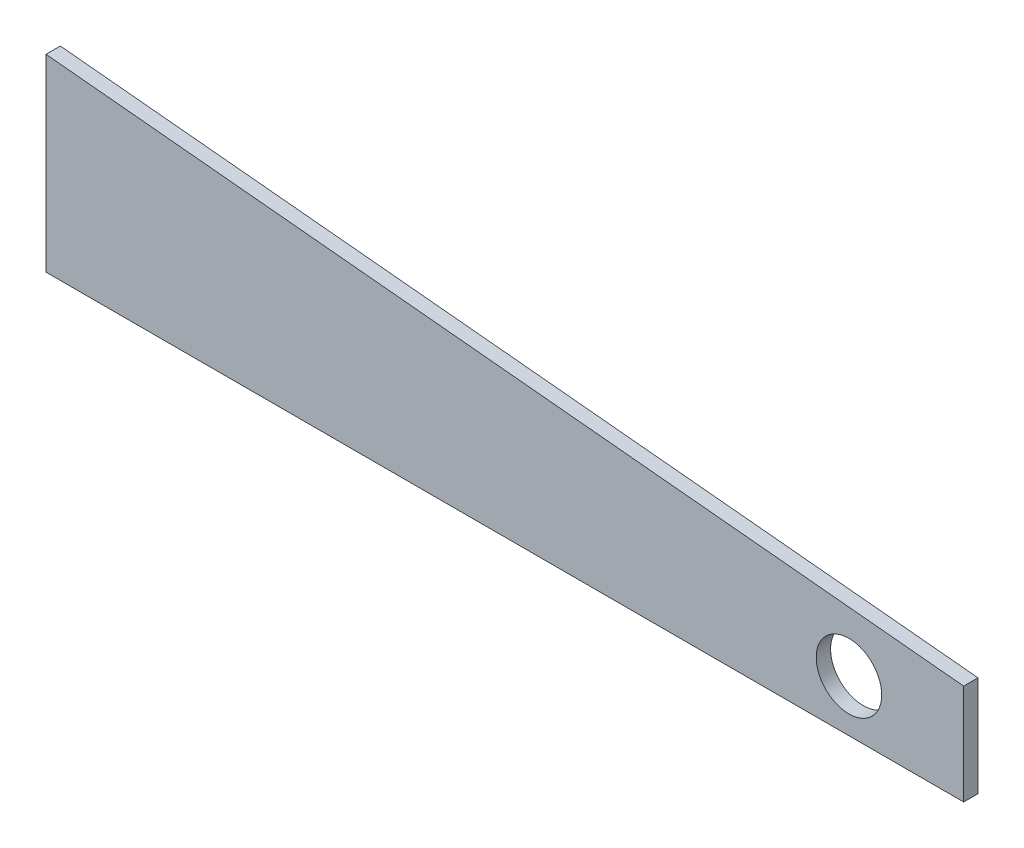
SolidWorks part; units mm, degrees
ref_plane "Front Plane" through (0, 0, 0) normal (0, 0, 1) x (1, 0, 0)
ref_plane "Top Plane" through (0, 0, 0) normal (0, 1, 0) x (1, 0, 0)
ref_plane "Right Plane" through (0, 0, 0) normal (1, 0, 0) x (0, 0, -1)
sketch "Sketch1" plane through (0, 0, 0) normal (0, 0, 1) x (1, 0, 0)
  line L0 (0, 0) -> (406.4, 0)
  line L1 (406.4, 0) -> (406.4, 44.45)
  line L2 (406.4, 44.45) -> (0, 83.566)
  line L3 (0, 83.566) -> (0, 0)
  dimension "D1" = 406.4
  dimension "D2" = 44.45
  dimension "D3" = 83.566
  dimension "D4" = 5.498
extrude "Boss-Extrude1" add sketch "Sketch1" along normal blind 6.35 contours L2 L3 L0 L1
sketch "Sketch2" plane through (0, 0, 6.35) normal (0, 0, 1) x (1, 0, 0)
  line L0 (0, 0) -> (406.4, 0) construction
  line L1 (406.4, 0) -> (406.4, 44.45) construction
  circle A0 centre (355.6, 22.86) radius 14.5
  dimension "D1" = 28.9999
  dimension "D2" = 22.86
  dimension "D3" = 50.8
extrude "Cut-Extrude1" cut sketch "Sketch2" against normal blind 6.35
